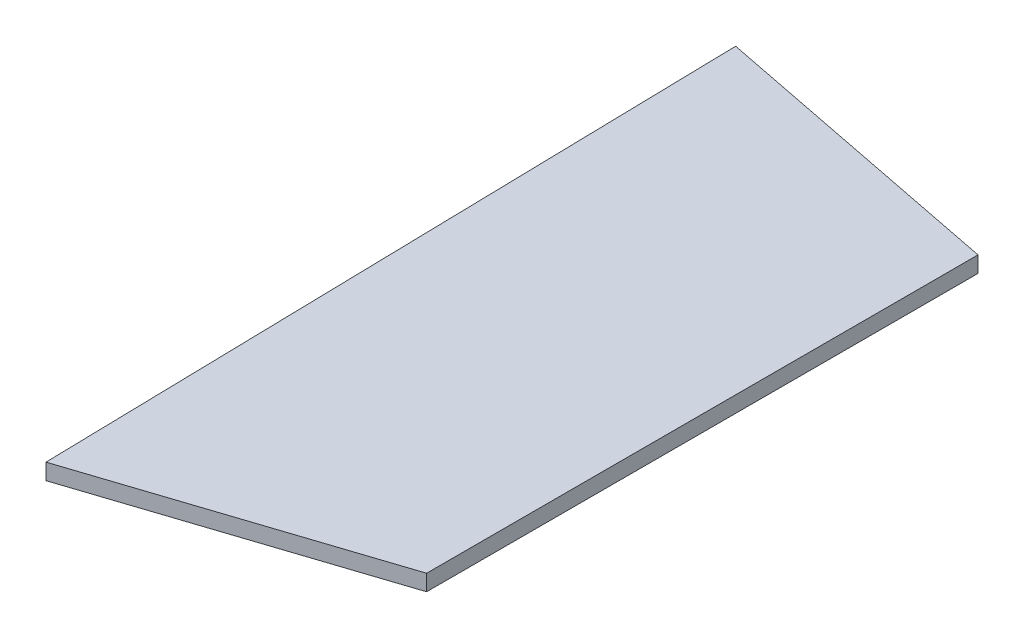
SolidWorks part; units mm, degrees
ref_plane "Plan de face" through (0, 0, 0) normal (0, 0, 1) x (1, 0, 0)
ref_plane "Plan de dessus" through (0, 0, 0) normal (0, 1, 0) x (1, 0, 0)
ref_plane "Plan de droite" through (0, 0, 0) normal (1, 0, 0) x (0, 0, -1)
sketch "Esquisse1" plane through (0, 0, 0) normal (0, 1, 0) x (1, 0, 0)
  line L0 (35.6489, 80.3077) -> (-1.9121, 87.7161)
  line L1 (-1.9121, 87.7161) -> (-1.8549, 85.0957)
  line L2 (-1.8549, 85.0957) -> (0, 0)
  line L3 (0, 0) -> (35.6489, 11.7058)
  line L4 (35.6489, 11.7058) -> (35.6489, 80.3077)
  point P5 (0, 0)
extrude "Boss.-Extru.1" add sketch "Esquisse1" along normal blind 2
